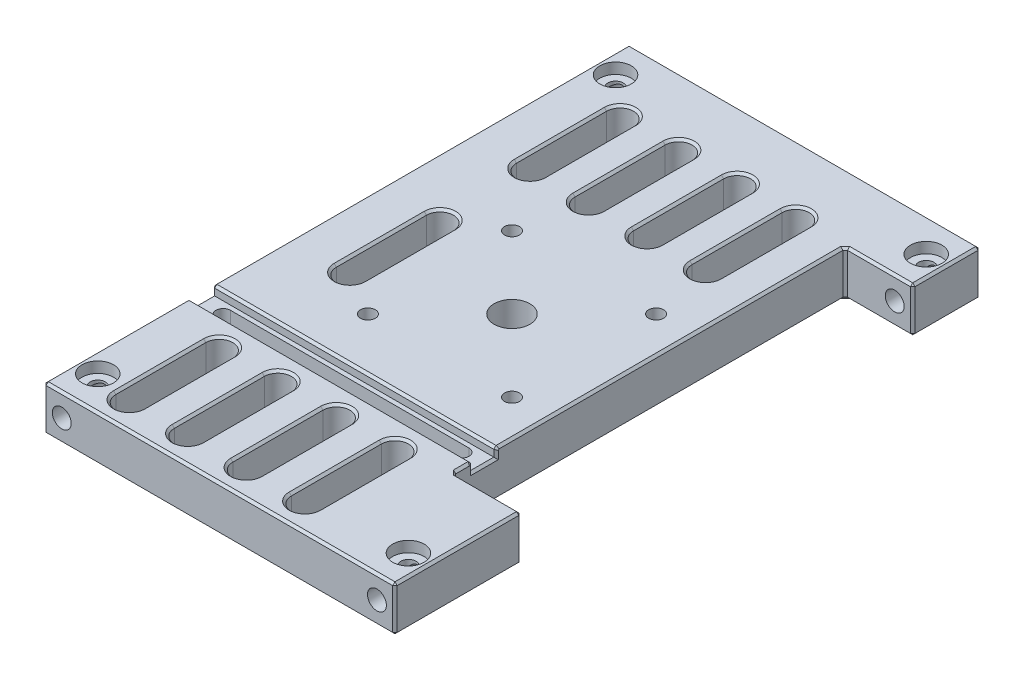
SolidWorks part; units mm, degrees
ref_plane "Plan de face" through (0, 0, 0) normal (0, 0, 1) x (1, 0, 0)
ref_plane "Plan de dessus" through (0, 0, 0) normal (0, 1, 0) x (1, 0, 0)
ref_plane "Plan de droite" through (0, 0, 0) normal (1, 0, 0) x (0, 0, -1)
sketch "Esquisse1" plane through (0, 0, 0) normal (0, 0, 1) x (1, 0, 0)
  line L1 (-39, 0.2172) -> (39, 0.2172)
  line L2 (-39, 0.2172) -> (-39, -9.7828)
  line L3 (-39, -9.7828) -> (39, -9.7828)
  line L4 (39, 0.2172) -> (39, -9.7828)
extrude "Boss.-Extru.1" add sketch "Esquisse1" along normal blind 130
sketch "Esquisse2" plane through (0, 0, 130) normal (0, 0, 1) x (1, 0, 0)
  line L0 (-52.4107, -4.7828) -> (51.3292, -4.7828) construction
  line L1 (39, 0.2172) -> (-39, 0.2172) construction
  line L2 (-35, 10.8156) -> (-35, -20.714) construction
  line L3 (35, 10.8156) -> (35, -20.714) construction
hole_wizard "Trou taraudé M5x0.81" positions "Esquisse3D1" profile "Esquisse3" tap size "M5x0.8" standard "Ansi Metric"
sketch3d "Esquisse3D1"
  line L0 (-52.4107, -4.7828, 130) -> (51.3292, -4.7828, 130) construction
  line L1 (-35, 10.8156, 130) -> (-35, -20.714, 130) construction
  line L2 (35, 10.8156, 130) -> (35, -20.714, 130) construction
  point P0 (-35, -4.7828, 130)
  point P6 (35, -4.7828, 130)
cosmetic thread "Filetage de perçage1" parameters "D1"=20, "D2"=5
cosmetic thread "Filetage de perçage2" parameters "D1"=20, "D2"=5
sketch "Esquisse3" plane through (-35, -4.7828, 130) normal (1, 0, 0) x (0, -1, 0)
  line L0 (0, 0) -> (0, 21.2618)
  line L1 (0, 21.2618) -> (2.1, 20)
  line L2 (2.1, 20) -> (2.1, 0)
  line L5 (2.1, 0) -> (0, 0)
  line L10 (0, 21.2618) -> (-2.1, 20) construction
  line L11 (0, -6.35) -> (0, 107.95) construction
  dimension "Diamètre du trou pour taraudage" = 4.2
  dimension "Profondeur du trou pour taraudage" = 20
  dimension "Angle de pointe" = 118
hole_wizard "Trou taraudé M5x0.82" positions "Esquisse4" profile "Esquisse5" tap size "M5x0.8" standard "Ansi Metric"
sketch "Esquisse4" plane through (0, 0, 0) normal (0, 0, -1) x (-1, 0, 0)
  line L0 (200052.4107, -4.7828) -> (-200051.3292, -4.7828) construction
  line L1 (-35, 10.8156) -> (-35, -20.714) construction
  line L2 (35, 10.8156) -> (35, -20.714) construction
  point P0 (-35, -4.7828)
  point P6 (35, -4.7828)
sketch "Esquisse5" plane through (35, -4.7828, 0) normal (1, 0, 0) x (0, 1, 0)
  line L0 (0, 0) -> (0, 21.2618)
  line L1 (0, 21.2618) -> (2.1, 20)
  line L2 (2.1, 20) -> (2.1, 0)
  line L5 (2.1, 0) -> (0, 0)
  line L10 (0, 21.2618) -> (-2.1, 20) construction
  line L11 (0, -6.35) -> (0, 107.95) construction
  dimension "Diamètre du trou pour taraudage" = 4.2
  dimension "Profondeur du trou pour taraudage" = 20
  dimension "Angle de pointe" = 118
cosmetic thread "Filetage de perçage6" parameters "D1"=19.2, "D2"=5.2
cosmetic thread "Filetage de perçage7" parameters "D1"=19.2, "D2"=5.2
sketch "Esquisse6" plane through (0, -9.7828, 0) normal (0, -1, 0) x (1, 0, 0)
  line L0 (0, -12.2103) -> (0, 141.5009) construction
  line L3 (-39, 0) -> (42.4498, 0) construction
  line L4 (-39, 130) -> (42.4498, 130) construction
  line L5 (-74.3135, 65) -> (67.5312, 65) construction
  dimension "D2" = 65
hole_wizard "Trou taraudé 3/8-161" positions "Esquisse3D2" profile "Esquisse8" tap size "3/8-16" standard "Ansi Inch" end condition through all
sketch3d "Esquisse3D2"
  line L0 (0, -9.7828, -12.2103) -> (0, -9.7828, 141.5009) construction
  line L1 (-74.3135, -9.7828, 65) -> (67.5312, -9.7828, 65) construction
  point P0 (0, -9.7828, 65)
sketch "Esquisse8" plane through (0, -9.7828, 65) normal (1, 0, 0) x (0, 0, -1)
  line L0 (0, 0) -> (0, 10)
  line L1 (0, 10) -> (3.9687, 10)
  line L2 (3.9687, 10) -> (3.9688, 0)
  line L5 (3.9688, 0) -> (0, 0)
  line L11 (0, -6.35) -> (0, 107.95) construction
  dimension "Diamètre du trou pour taraudage jusqu'au prochain" = 7.9375
  dimension "Profondeur du trou pour taraudage jusqu'au prochain" = 10
cosmetic thread "Filetage de perçage5" parameters "D2"=9.525
sketch "Esquisse9" plane through (0, 0.2172, 0) normal (0, 1, 0) x (1, 0, 0)
  line L0 (39, -130) -> (-39, -130) construction
  line L1 (52.6528, -102) -> (24, -102)
  line L2 (52.6528, -102) -> (52.6528, -15)
  line L3 (52.6528, -15) -> (24, -15)
  line L4 (24, -102) -> (24, -15)
  line L6 (39, -130) -> (39, 0) construction
  dimension "D1" = 28
  dimension "D2" = 87
  dimension "D3" = 15
extrude "Enlèv. mat.-Extru.1" cut sketch "Esquisse9" against normal through all
sketch "Esquisse10" plane through (0, 0.2172, 0) normal (0, 1, 0) x (1, 0, 0)
  line L0 (39, -130) -> (-39, -130) construction
  line L1 (-43.7628, -97.75) -> (24.7857, -97.75)
  line L2 (-43.7628, -97.75) -> (-43.7628, -92.55)
  line L3 (-43.7628, -92.55) -> (24.7857, -92.55)
  line L4 (24.7857, -97.75) -> (24.7857, -92.55)
  dimension "D1" = 32.25
  dimension "D2" = 5.2
extrude "Enlèv. mat.-Extru.2" cut sketch "Esquisse10" against normal blind 2
chamfer "Chanfrein1" distance 0.5 angle 45 2 edges at (-7.5, 0.2172, 92.55) (-7.5, 0.2172, 97.75)
sketch "Esquisse11" plane through (0, -1.7828, 0) normal (0, 1, 0) x (1, 0, 0)
  line L0 (-50.2283, -95.15) -> (28.7282, -95.15) construction
  line L1 (-39, -97.75) -> (24, -97.75) construction
  dimension "D1" = 2.6
sketch "Esquisse12" plane through (0, -9.7828, 0) normal (0, -1, 0) x (-1, 0, 0)
  line L0 (-19, -134.9988) -> (-19, 7.4723) construction
  line L1 (-24, -15) -> (-24, -102) construction
  line L2 (34, -134.9988) -> (34, 7.4723) construction
  line L3 (39, -130) -> (39, 0) construction
  line L4 (-19, -95.15) -> (34, -95.15) construction
  line L5 (50.2283, -95.15) -> (-28.7282, -95.15) construction
  line L6 (-19, -93.55) -> (34, -93.55)
  line L7 (-19, -96.75) -> (34, -96.75)
  line L8 (39, -130) -> (-39, -130) construction
  arc A0 (-19, -93.55) -> (-19, -96.75) centre (-19, -95.15) ccw
  arc A1 (34, -96.75) -> (34, -93.55) centre (34, -95.15) ccw
  point P12 (7.5, -95.15)
  dimension "D3" = 34.85
  dimension "D1" = 5
  dimension "D2" = 5
extrude "Enlèv. mat.-Extru.3" cut sketch "Esquisse12" against normal through all
sketch "Esquisse13" plane through (0, -9.7828, 0) normal (0, -1, 0) x (-1, 0, 0)
  line L0 (34, -134.3696) -> (34, -47.7711) construction
  line L1 (39, -130) -> (39, 0) construction
  line L2 (-19, -132.6072) -> (-19, -60.3895) construction
  line L3 (-24, -15) -> (-24, -102) construction
  line L4 (-19, -95.15) -> (34, -95.15) construction
  line L5 (50.2283, -95.15) -> (-28.7282, -95.15) construction
  line L6 (-19, -92.15) -> (34, -92.15)
  line L7 (-19, -98.15) -> (34, -98.15)
  arc A0 (-19, -92.15) -> (-19, -98.15) centre (-19, -95.15) ccw
  arc A1 (34, -98.15) -> (34, -92.15) centre (34, -95.15) ccw
  point P13 (7.5, -95.15)
  dimension "D1" = 5
  dimension "D2" = 5
extrude "Enlèv. mat.-Extru.4" cut sketch "Esquisse13" against normal blind 3.5
sketch "Esquisse14" plane through (0, -9.7828, 0) normal (0, -1, 0) x (1, 0, 0)
  line L0 (0, -5.9074) -> (0, 139.621) construction
  line L1 (0, 65) -> (-42.1968, 65) construction
  line L2 (-46.3723, 49) -> (38.9798, 49) construction
  line L3 (-46.3723, 81) -> (38.9798, 81) construction
  line L4 (-16, 39.6547) -> (-16, 89.7606) construction
  line L5 (16, 33.5142) -> (16, 89.7606) construction
  dimension "D1" = 16
  dimension "D2" = 16
  dimension "D3" = 16
  dimension "D4" = 16
hole_wizard "Trou taraudé M4x0.71" positions "Esquisse3D3" profile "Esquisse15" tap size "M4x0.7" standard "Ansi Metric" end condition up to next
sketch3d "Esquisse3D3"
  line L0 (-46.3723, -9.7828, 49) -> (38.9798, -9.7828, 49) construction
  line L1 (-16, -9.7828, 39.6547) -> (-16, -9.7828, 89.7606) construction
  line L2 (-46.3723, -9.7828, 81) -> (38.9798, -9.7828, 81) construction
  line L3 (16, -9.7828, 33.5142) -> (16, -9.7828, 89.7606) construction
  point P0 (-16, -9.7828, 49)
  point P6 (-16, -9.7828, 81)
  point P10 (16, -9.7828, 81)
  point P14 (16, -9.7828, 49)
sketch "Esquisse15" plane through (-16, -9.7828, 49) normal (1, 0, 0) x (0, 0, -1)
  line L0 (0, 0) -> (0, 10)
  line L1 (0, 10) -> (1.65, 10)
  line L2 (1.65, 10) -> (1.65, 0)
  line L5 (1.65, 0) -> (0, 0)
  line L11 (0, -6.35) -> (0, 107.95) construction
  dimension "Diamètre du trou pour taraudage jusqu'au prochain" = 3.3
  dimension "Profondeur du trou pour taraudage jusqu'au prochain" = 10
cosmetic thread "Filetage de perçage8" parameters "D2"=4
cosmetic thread "Filetage de perçage9" parameters "D2"=4
cosmetic thread "Filetage de perçage10" parameters "D2"=4
cosmetic thread "Filetage de perçage11" parameters "D2"=4
sketch "Esquisse16" plane through (0, 0.2172, 0) normal (0, 1, 0) x (1, 0, 0)
  line L0 (-34.5, -144.3986) -> (-34.5, 33.066) construction
  line L1 (34.5, -144.3986) -> (34.5, 33.066) construction
  line L2 (-51.5319, -122.5) -> (51.5622, -122.5) construction
  line L3 (39, -130) -> (-39, -130) construction
  line L4 (-51.5319, -7.5) -> (51.5622, -7.5) construction
  line L5 (39, 0) -> (-39, 0) construction
  dimension "D1" = 34.5
  dimension "D2" = 69
  dimension "D3" = 7.5
  dimension "D4" = 7.5
hole_wizard "Chambrage pour vis à tête ronde bombée M32" positions "Esquisse21" profile "Esquisse20" counterbore size "M3" standard "Ansi Metric" end condition through all
sketch "Esquisse21" plane through (0, 0.2172, 0) normal (0, 1, 0) x (1, 0, 0)
  line L0 (-34.5, -144.3986) -> (-34.5, 33.066) construction
  line L1 (-51.5319, -122.5) -> (51.5622, -122.5) construction
  line L2 (34.5, -144.3986) -> (34.5, 33.066) construction
  line L3 (-51.5319, -7.5) -> (51.5622, -7.5) construction
  point P0 (-34.5, -122.5)
  point P6 (34.5, -122.5)
  point P10 (-34.5, -7.5)
  point P14 (34.5, -7.5)
sketch "Esquisse20" plane through (-34.5, 0.2172, 122.5) normal (1, 0, 0) x (0, 0, 1)
  line L0 (0, 0) -> (0, 10)
  line L1 (0, 10) -> (1.7, 10)
  line L3 (1.7, 10) -> (1.7, 2.4)
  line L4 (1.7, 2.4) -> (3.5, 2.4)
  line L5 (3.5, 2.4) -> (3.5, 0)
  line L7 (3.5, 0) -> (0, 0)
  line L11 (0, -6.35) -> (0, 107.95) construction
  dimension "Diamètre du perçage jusqu'au prochain" = 3.4
  dimension "Profondeur du perçage jusqu'au prochain" = 10
  dimension "Diamètre du chambrage" = 7
  dimension "Profondeur du chambrage" = 2.4
sketch "Esquisse22" plane through (0, -9.7828, 0) normal (0, -1, 0) x (1, 0, 0)
  line L0 (-26, -8.996) -> (-26, 158.238) construction
  line L1 (-39, 130) -> (-39, 0) construction
  line L2 (-13, -8.996) -> (-13, 158.238) construction
  line L3 (0, -7.3645) -> (0, 158.238) construction
  line L4 (13, -7.3645) -> (13, 158.238) construction
  line L5 (39, 15) -> (39, 0) construction
  line L6 (26, -7.3645) -> (26, 158.238) construction
  line L7 (-57.2229, 25) -> (53.2331, 25) construction
  line L8 (-57.2229, 65) -> (54.212, 65) construction
  line L9 (-39, 0) -> (39, 0) construction
  line L10 (-57.2229, 114) -> (54.212, 114) construction
  line L12 (-26, 55) -> (-26, 75) construction
  line L17 (-29, 55) -> (-29, 75)
  line L18 (-23, 55) -> (-23, 75)
  line L19 (-26, 15) -> (-26, 35) construction
  line L20 (-29, 15) -> (-29, 35)
  line L21 (-23, 15) -> (-23, 35)
  line L22 (-13, 15) -> (-13, 35) construction
  line L23 (-16, 15) -> (-16, 35)
  line L24 (-10, 15) -> (-10, 35)
  line L25 (0, 15) -> (0, 35) construction
  line L26 (-3, 15) -> (-3, 35)
  line L27 (3, 15) -> (3, 35)
  line L28 (13, 15) -> (13, 35) construction
  line L29 (10, 15) -> (10, 35)
  line L30 (16, 15) -> (16, 35)
  line L31 (-26, 104) -> (-26, 124) construction
  line L32 (-29, 104) -> (-29, 124)
  line L33 (-23, 104) -> (-23, 124)
  line L34 (-13, 104) -> (-13, 124) construction
  line L35 (-16, 104) -> (-16, 124)
  line L36 (-10, 104) -> (-10, 124)
  line L37 (0, 104) -> (0, 124) construction
  line L38 (-3, 104) -> (-3, 124)
  line L39 (3, 104) -> (3, 124)
  line L40 (13, 104) -> (13, 124) construction
  line L41 (10, 104) -> (10, 124)
  line L42 (16, 104) -> (16, 124)
  arc A4 (-29, 55) -> (-23, 55) centre (-26, 55) ccw
  arc A5 (-23, 75) -> (-29, 75) centre (-26, 75) ccw
  arc A6 (-29, 15) -> (-23, 15) centre (-26, 15) ccw
  arc A7 (-23, 35) -> (-29, 35) centre (-26, 35) ccw
  arc A8 (-16, 15) -> (-10, 15) centre (-13, 15) ccw
  arc A9 (-10, 35) -> (-16, 35) centre (-13, 35) ccw
  arc A10 (-3, 15) -> (3, 15) centre (0, 15) ccw
  arc A11 (3, 35) -> (-3, 35) centre (0, 35) ccw
  arc A12 (10, 15) -> (16, 15) centre (13, 15) ccw
  arc A13 (16, 35) -> (10, 35) centre (13, 35) ccw
  arc A14 (-29, 104) -> (-23, 104) centre (-26, 104) ccw
  arc A15 (-23, 124) -> (-29, 124) centre (-26, 124) ccw
  arc A16 (-16, 104) -> (-10, 104) centre (-13, 104) ccw
  arc A17 (-10, 124) -> (-16, 124) centre (-13, 124) ccw
  arc A18 (-3, 104) -> (3, 104) centre (0, 104) ccw
  arc A19 (3, 124) -> (-3, 124) centre (0, 124) ccw
  arc A20 (10, 104) -> (16, 104) centre (13, 104) ccw
  arc A21 (16, 124) -> (10, 124) centre (13, 124) ccw
  point P26 (-26, 65)
  point P34 (-26, 25)
  point P41 (-13, 25)
  point P48 (0, 25)
  point P54 (13, 25)
  point P62 (-26, 114)
  point P67 (-13, 114)
  point P73 (0, 114)
  point P80 (13, 114)
  dimension "D8" = 6
  dimension "D10" = 6
  dimension "D12" = 6
  dimension "D1" = 13
  dimension "D2" = 26
  dimension "D3" = 26
  dimension "D4" = 13
  dimension "D5" = 25
  dimension "D6" = 65
  dimension "D7" = 114
  dimension "D9" = 20
  dimension "D11" = 20
  dimension "D13" = 20
  dimension "D14" = 6
  dimension "D15" = 20
  dimension "D16" = 6
  dimension "D17" = 20
  dimension "D18" = 6
  dimension "D19" = 20
  dimension "D20" = 6
  dimension "D21" = 20
  dimension "D22" = 6
  dimension "D23" = 20
  dimension "D24" = 6
  dimension "D25" = 20
extrude "Enlèv. mat.-Extru.5" cut sketch "Esquisse22" against normal blind 10
chamfer "Chanfrein2" distance 0.5 angle 45 36 edges at (-39, -0.0328, 98) (-39, -1.0328, 97.75) (-39, -1.7828, 95.15) (-39, -1.0328, 92.55) (-39, -0.0328, 92.3) (-39, 0.2172, 114.125) (-39, -4.7828, 130) (0, -9.7828, 130) (0, 0.2172, 130) (39, -9.7828, 116) (39, -4.7828, 130) (39, 0.2172, 116) (39, -4.7828, 102) (24, -4.7828, 15) (24, -4.7828, 102) (39, -4.7828, 0) (0, -9.7828, 0) (-39, -9.7828, 65) (-39, 0.2172, 46.025) (-39, -4.7828, 0) (0, 0.2172, 0) (39, -9.7828, 7.5) (39, 0.2172, 7.5) (31.5, -9.7828, 102) (24, -9.7828, 58.5) (31.5, -9.7828, 15) (39, -4.7828, 15) (31.5, 0.2172, 15) (24, 0.2172, 53.525) (24, -0.0328, 92.3) (24, -1.0328, 92.55) (24, -1.7828, 95.15) (24, -1.0328, 97.75) (24, -0.0328, 98) (24, 0.2172, 100.125) (31.5, 0.2172, 102)
chamfer "Chanfrein3" distance 0.5 angle 45 72 edges at (-26, -9.7828, 38) (-29, -9.7828, 25) (-26, -9.7828, 12) (-23, -9.7828, 25) (-16, -9.7828, 25) (-13, -9.7828, 38) (-10, -9.7828, 25) (-13, -9.7828, 12) (0, -9.7828, 12) (-3, -9.7828, 25) (0, -9.7828, 38) (3, -9.7828, 25) (13, -9.7828, 38) (10, -9.7828, 25) (13, -9.7828, 12) (16, -9.7828, 25) (-26, -9.7828, 78) (-29, -9.7828, 65) (-26, -9.7828, 52) (-23, -9.7828, 65) (-26, -9.7828, 127) (-29, -9.7828, 114) (-26, -9.7828, 101) (-23, -9.7828, 114) (-13, -9.7828, 127) (-16, -9.7828, 114) (-10, -9.7828, 114) (-13, -9.7828, 101) (0, -9.7828, 101) (-3, -9.7828, 114) (0, -9.7828, 127) (3, -9.7828, 114) (13, -9.7828, 127) (10, -9.7828, 114) (13, -9.7828, 101) (16, -9.7828, 114) (13, 0.2172, 101) (16, 0.2172, 114) (13, 0.2172, 127) (10, 0.2172, 114) (0, 0.2172, 127) (3, 0.2172, 114) (0, 0.2172, 101) (-3, 0.2172, 114) (-13, 0.2172, 127) (-10, 0.2172, 114) (-16, 0.2172, 114) (-13, 0.2172, 101) (-26, 0.2172, 101) (-23, 0.2172, 114) (-26, 0.2172, 127) (-29, 0.2172, 114) (-26, 0.2172, 78) (-23, 0.2172, 65) (-26, 0.2172, 52) (-29, 0.2172, 65) (13, 0.2172, 12) (16, 0.2172, 25) (13, 0.2172, 38) (10, 0.2172, 25) (0, 0.2172, 38) (3, 0.2172, 25) (-3, 0.2172, 25) (0, 0.2172, 12) (-13, 0.2172, 12) (-10, 0.2172, 25) (-13, 0.2172, 38) (-16, 0.2172, 25) (-26, 0.2172, 38) (-23, 0.2172, 25) (-26, 0.2172, 12) (-29, 0.2172, 25)
equation "\"D3@Esquisse1\"= \"D1@Esquisse1\" * 2"
equation "\"D3@Esquisse2\"= \"D2@Esquisse2\""
